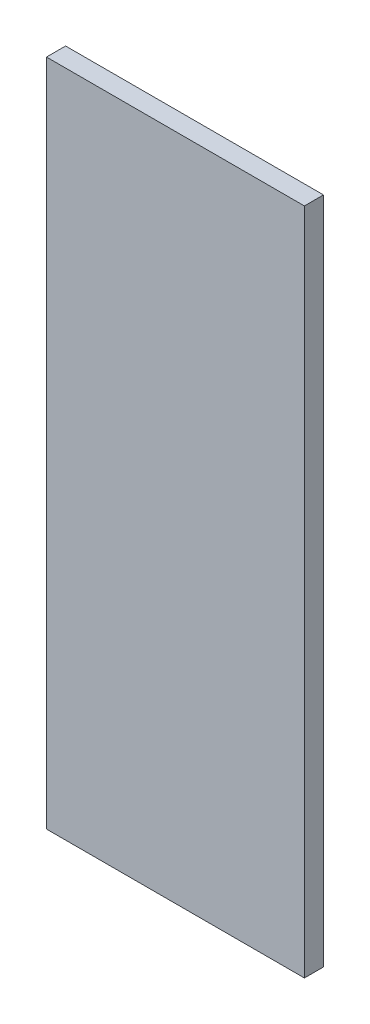
SolidWorks part; units mm, degrees
ref_plane "Front Plane" through (0, 0, 0) normal (0, 0, 1) x (1, 0, 0)
ref_plane "Top Plane" through (0, 0, 0) normal (0, 1, 0) x (1, 0, 0)
ref_plane "Right Plane" through (0, 0, 0) normal (1, 0, 0) x (0, 0, -1)
sketch "Sketch3" plane through (0, 0, 0) normal (0, 0, 1) x (1, 0, 0)
  line L1 (0, 0) -> (-135, 0)
  line L2 (0, 0) -> (0, 350)
  line L3 (0, 350) -> (-135, 350)
  line L4 (-135, 0) -> (-135, 350)
  dimension "D1" = 350
  dimension "D2" = 135
extrude "Boss-Extrude1" add sketch "Sketch3" along normal blind 10
